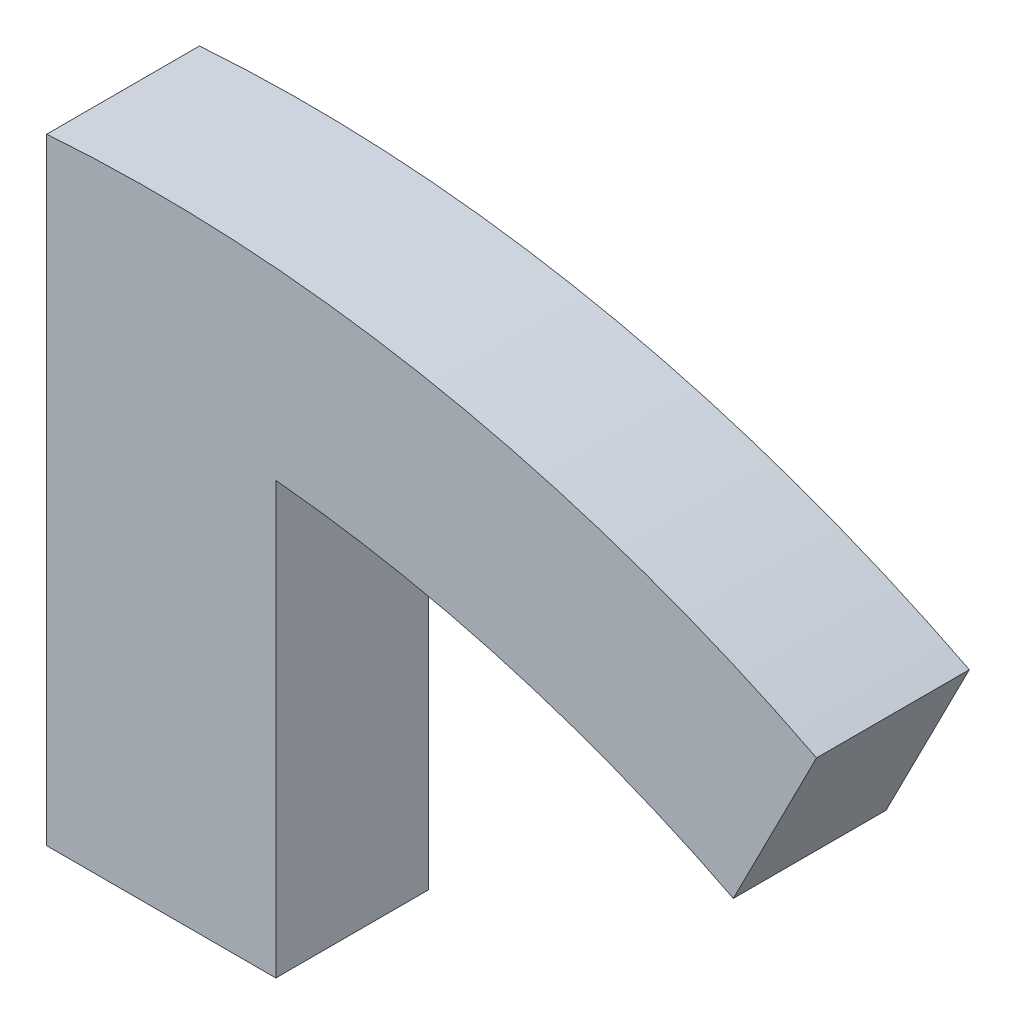
SolidWorks part; units mm, degrees
ref_plane "Front Plane" through (0, 0, 0) normal (0, 0, 1) x (1, 0, 0)
ref_plane "Top Plane" through (0, 0, 0) normal (0, 1, 0) x (1, 0, 0)
ref_plane "Right Plane" through (0, 0, 0) normal (1, 0, 0) x (0, 0, -1)
sketch "Sketch1" plane through (0, 0, 0) normal (0, 0, 1) x (1, 0, 0)
  line L0 (0, 0) -> (0, 35.8535) construction
  line L1 (0, 55) -> (0, 83.6) construction
  line L2 (37.9536, 74.4881) -> (43.4015, 85.1802)
  line L3 (0, 55) -> (-7, 55)
  line L4 (-7, 55) -> (-7, 95.3434)
  line L5 (8, 83.2163) -> (8, 55)
  line L6 (0, 55) -> (8, 55)
  circle A0 centre (0, 0) radius 83.6 construction
  circle A1 centre (0, 0) radius 55 construction
  arc A2 (-7, 95.3434) -> (43.4015, 85.1802) centre (0, 0) cw
  arc A3 (8, 83.2163) -> (37.9536, 74.4881) centre (0, 0) cw
  dimension "D1" = 167.2
  dimension "D2" = 110
  dimension "D3" = 12
  dimension "D4" = 7
  dimension "D5" = 27
  dimension "D6" = 8
extrude "Boss-Extrude1" add sketch "Sketch1" along normal mid plane 10
